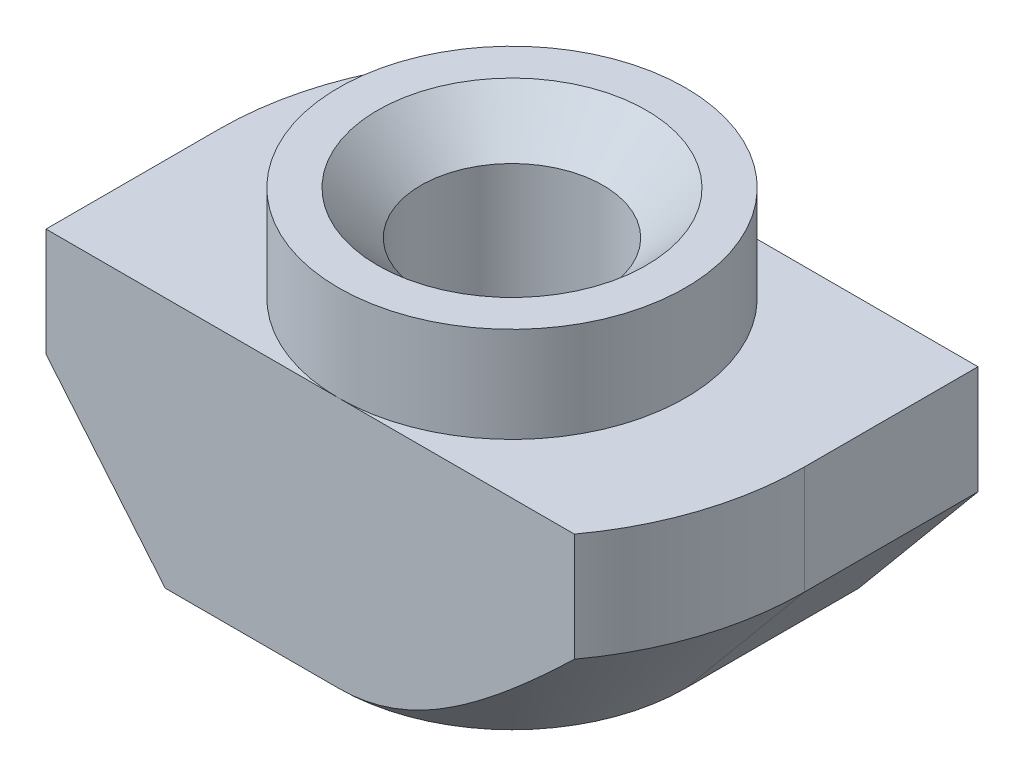
SolidWorks part; units mm, degrees
material "Сталь 20  ГОСТ 1050-2013"
ref_plane "Спереди" through (0, 0, 0) normal (0, 0, 1) x (1, 0, 0)
ref_plane "Сверху" through (0, 0, 0) normal (0, 1, 0) x (1, 0, 0)
ref_plane "Справа" through (0, 0, 0) normal (1, 0, 0) x (0, 0, -1)
sketch "Эскиз1" plane through (0, 0, 0) normal (0, 0, 1) x (1, 0, 0)
  line L0 (4, 0) -> (-4, 0)
  line L1 (-4, 0) -> (-4, -2.2)
  line L2 (-4, -2.2) -> (-6.75, -2.2)
  line L3 (-6.75, -2.2) -> (-6.75, -8)
  line L4 (-6.75, -8) -> (6.75, -8)
  line L5 (0, -8) -> (0, 0) construction
  line L6 (6.75, -2.2) -> (6.75, -8)
  line L7 (4, -2.2) -> (6.75, -2.2)
  line L8 (4, 0) -> (4, -2.2)
  dimension "D1" = 8
  dimension "D2" = 13.5
  dimension "D3" = 8
  dimension "D4" = 2.2
extrude "Бобышка-Вытянуть1" add sketch "Эскиз1" along normal mid plane 8
hole_wizard "Отверстие обработанное метчиком M51" positions "Эскиз2" profile "Эскиз3" tap size "M5" standard "ISO" end condition up to next
sketch "Эскиз2" plane through (0, 0, 0) normal (0, 1, 0) x (1, 0, 0)
  point P0 (0, 0)
sketch "Эскиз3" plane through (0, 0, 0) normal (1, 0, 0) x (0, 0, 1)
  line L0 (0, 0) -> (0, 8)
  line L1 (0, 8) -> (3.1, 8)
  line L2 (2.1, 7) -> (2.1, 1)
  line L3 (2.1, 1) -> (3.1, 0)
  line L5 (3.1, 0) -> (0, 0)
  line L6 (-2.1, 1) -> (-3.1, 0) construction
  line L7 (3.1, 8) -> (2.1, 7)
  line L8 (-3.1, 8) -> (-2.1, 7) construction
  line L11 (0, -6.35) -> (0, 107.95) construction
  dimension "Диаметр проходного сверла" = 4.2
  dimension "Глубина проходного сверла" = 8
  dimension "Диаметр передней зенковки" = 6.2
  dimension "Угол передней зенковки" = 90
  dimension "Диаметр задней зенковки" = 6.2
  dimension "Угол задней зенковки" = 90
cosmetic thread "Отверстие резьбы2" parameters "D2"=5
sketch "Эскиз4" plane through (0, 0, 0) normal (0, 1, 0) x (1, 0, 0)
  line L8 (-4, -4) -> (-4, 4) construction
  circle A2 centre (0, 0) radius 4
extrude "Вырез-Вытянуть1" cut sketch "Эскиз4" against normal up to surface (2.2 mm away) flip side to cut up to face at (-5.375, -2.2, 0)
sketch "Эскиз5" plane through (0, -2.2, 0) normal (0, 1, 0) x (1, 0, 0)
  line L0 (-6.75, 0) -> (-6.75, 4)
  line L1 (-6.75, -4) -> (-6.75, 4) construction
  line L2 (-6.75, 4) -> (-5.4371, 4)
  line L3 (0, 4) -> (-6.75, 4) construction
  line L4 (6.75, 0) -> (6.75, -4)
  line L5 (6.75, -4) -> (6.75, 4) construction
  line L6 (6.75, -4) -> (5.4371, -4)
  line L7 (6.75, -4) -> (0, -4) construction
  arc A0 (-5.4371, 4) -> (-6.75, 0) centre (0, 0) ccw
  arc A2 (6.75, 0) -> (5.4371, -4) centre (0, 0) cw
extrude "Вырез-Вытянуть2" cut sketch "Эскиз5" against normal through all
sketch "Эскиз6" plane through (0, 0, 4) normal (0, 0, 1) x (1, 0, 0)
  line L0 (-6.75, -4.7) -> (-6.75, -8)
  line L1 (-6.75, -2.2) -> (-6.75, -8) construction
  line L2 (-6.75, -8) -> (-4, -8)
  line L3 (-6.75, -8) -> (5.4371, -8) construction
  line L4 (-4, -8) -> (-6.75, -4.7)
  line L5 (0, -2.2) -> (-6.75, -2.2) construction
  line L7 (-4, 0) -> (-4, -2.2) construction
  point P10 (0, 0)
  dimension "D1" = 2.5
sketch "Эскиз7" plane through (0, -8, 0) normal (0, -1, 0) x (1, 0, 0)
  line L0 (0, 6.75) -> (-6.75, 6.75)
  line L1 (-6.75, 6.75) -> (-6.75, 0)
  line L2 (0, -6.75) -> (6.75, -6.75)
  line L3 (6.75, -6.75) -> (6.75, 0)
  arc A0 (-6.75, 0) -> (0, -6.75) centre (0, 0) ccw
  arc A1 (6.75, 0) -> (0, 6.75) centre (0, 0) ccw
sweep "Вырез-По траектории1" cut profiles "Эскиз6" path "Эскиз7"
